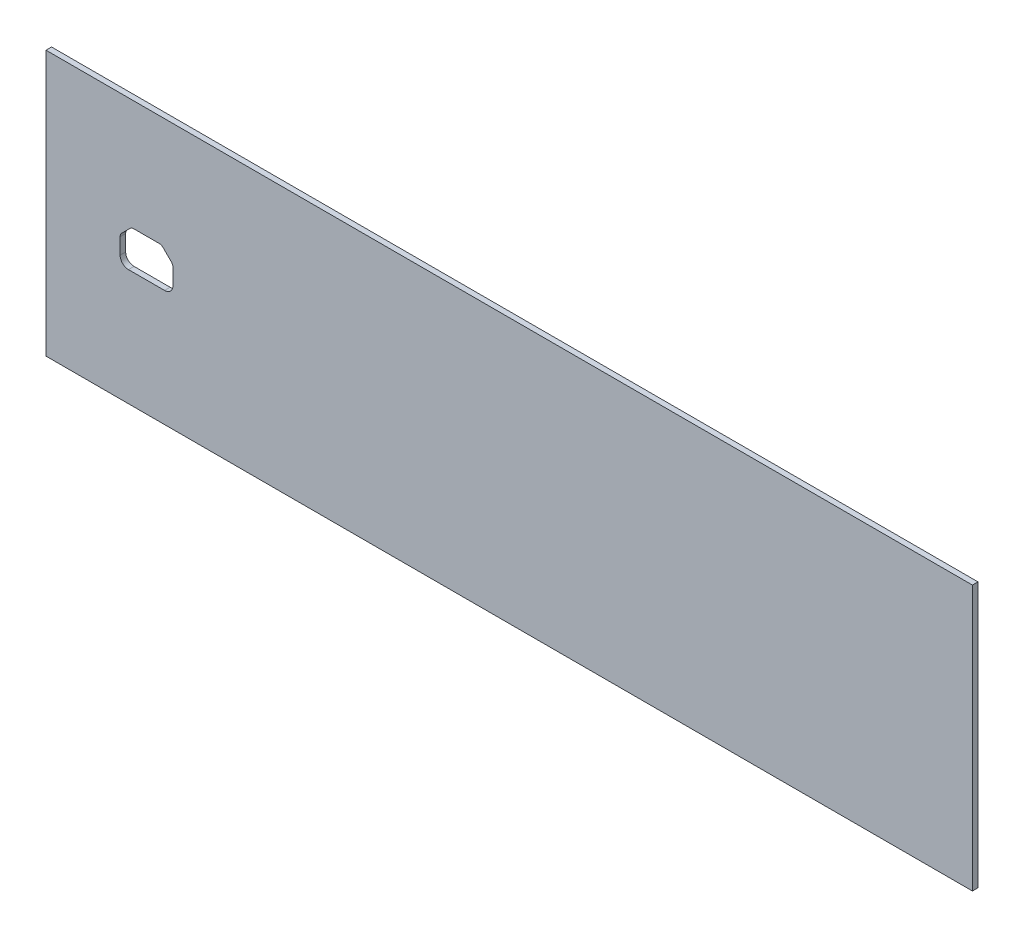
SolidWorks part; units mm, degrees
ref_plane "Front Plane" through (0, 0, 0) normal (0, 0, 1) x (1, 0, 0)
ref_plane "Top Plane" through (0, 0, 0) normal (0, 1, 0) x (1, 0, 0)
ref_plane "Right Plane" through (0, 0, 0) normal (1, 0, 0) x (0, 0, -1)
sketch "Sketch1" plane through (0, 0, 0) normal (0, 0, 1) x (1, 0, 0)
  line L0 (-250, -71.5) -> (-250, 68.5)
  line L1 (-250, 68.5) -> (-250, 71.5)
  line L2 (-250, 71.5) -> (250, 71.5)
  line L3 (250, 71.5) -> (250, -71.5)
  line L4 (250, -71.5) -> (-250, -71.5)
extrude "Boss-Extrude1" add sketch "Sketch1" along normal blind 3
sketch "Sketch2" plane through (0, 0, 3) normal (0, 0, 1) x (1, 0, 0)
  line L0 (-250, 0) -> (-210, 0)
  line L1 (-250, 71.5) -> (-250, -71.5) construction
  line L2 (-209.1213, 6.4142) -> (-204.7071, 10.8284)
  line L3 (-210, -4.2929) -> (-210, 4.2929)
  line L4 (-186, -8.7929) -> (-205.5, -8.7929)
  line L5 (-181.5, 4.2929) -> (-181.5, -4.2929)
  line L6 (-186.7929, 10.8284) -> (-182.3787, 6.4142)
  line L7 (-202.5858, 11.7071) -> (-188.9142, 11.7071)
  arc A0 (-202.5858, 11.7071) -> (-204.7071, 10.8284) centre (-202.5858, 8.7071) ccw
  arc A1 (-209.1213, 6.4142) -> (-210, 4.2929) centre (-207, 4.2929) ccw
  arc A2 (-210, -4.2929) -> (-205.5, -8.7929) centre (-205.5, -4.2929) ccw
  arc A3 (-186, -8.7929) -> (-181.5, -4.2929) centre (-186, -4.2929) ccw
  arc A4 (-181.5, 4.2929) -> (-182.3787, 6.4142) centre (-184.5, 4.2929) ccw
  arc A5 (-186.7929, 10.8284) -> (-188.9142, 11.7071) centre (-188.9142, 8.7071) ccw
extrude "Cut-Extrude2" cut sketch "Sketch2" against normal up to surface (3 mm away) contours L6 A5 L7 A0 L2 A1 L3 A2 L4 A3 L5 A4 up to face at (0, 0, 0)
